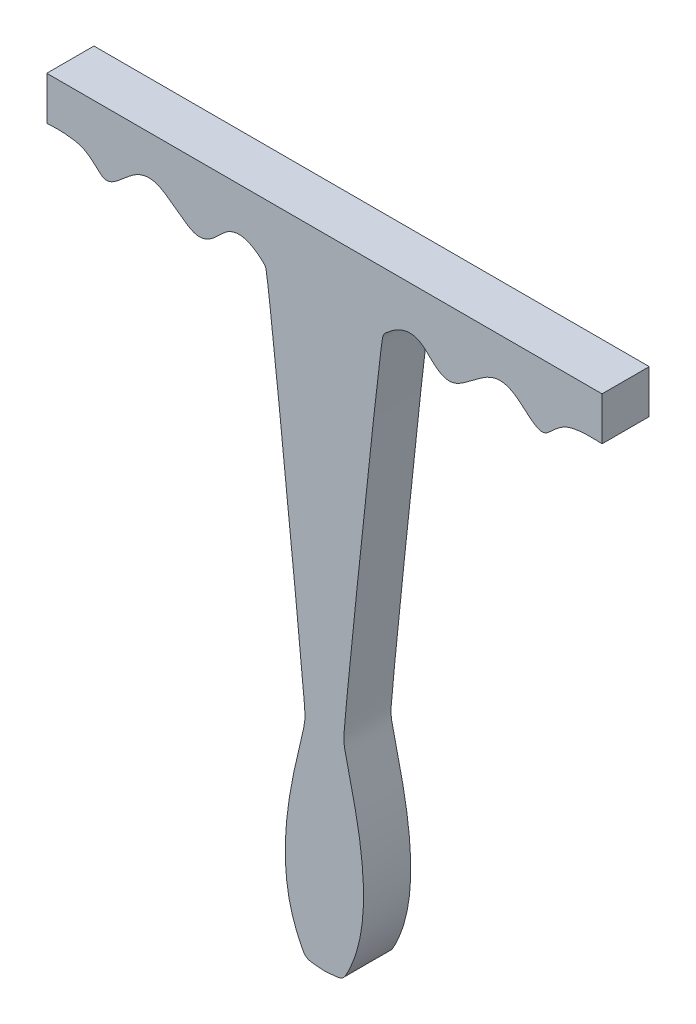
SolidWorks part; units mm, degrees
ref_plane "Plan de face" through (0, 0, 0) normal (0, 0, 1) x (1, 0, 0)
ref_plane "Plan de dessus" through (0, 0, 0) normal (0, 1, 0) x (1, 0, 0)
ref_plane "Plan de droite" through (0, 0, 0) normal (1, 0, 0) x (0, 0, -1)
sketch "Esquisse1" plane through (0, 0, 0) normal (0, 0, 1) x (1, 0, 0)
  line L0 (0, 0) -> (0, 1.7852) construction
  line L1 (0, 0) -> (0, 29.7342) construction
  line L2 (50, 24.2025) -> (-50, 24.2025)
  line L3 (-50, 24.2025) -> (-50, 16.4025)
  line L4 (50, 24.2025) -> (50, 16.4025)
  spline S0 degree 3 poles (-50, 16.4025) (-49.8421, 16.3861) (-42.4038, 17.1358) (-39.6187, 10.7861) (-33.9349, 17.4991) (-30.5564, 17.2857) (-26.8963, 14.9522) (-21.7768, 10.2494) (-16.6861, 18.7924) (-10.7283, 14.0803) (-10.0954, 12.8318) (-3.567, -49.8091) (-3.3281, -55.5258) (-9.9956, -75.8742) (-3.4964, -90.6478) (-2.9323, -90.597) (0, -90.7975) knots 0 0 0 0 0.017427 0.034313 0.051765 0.072769 0.077743 0.1015 0.145977 0.215724 0.261466 0.565409 0.636791 0.903902 0.943562 1 1 1 1
  spline S1 degree 3 poles (50, 16.4025) (49.8421, 16.3861) (42.4038, 17.1358) (39.6187, 10.7861) (33.9349, 17.4991) (30.5564, 17.2857) (26.8963, 14.9522) (21.7768, 10.2494) (16.6861, 18.7924) (10.7283, 14.0803) (10.0954, 12.8318) (3.567, -49.8091) (3.3281, -55.5258) (9.9956, -75.8742) (3.4964, -90.6478) (2.9323, -90.597) (0, -90.7975) knots 0 0 0 0 0.017427 0.034313 0.051765 0.072769 0.077743 0.1015 0.145977 0.215724 0.261466 0.565409 0.636791 0.903902 0.943562 1 1 1 1
  point P17 (0, 24.2025)
  dimension "D1" = 50
  dimension "D2" = 7.8
  dimension "D3" = 4.25
  dimension "D4" = 3.5
  dimension "D5" = 2
  dimension "D6" = 115
extrude "Boss.-Extru.1" add sketch "Esquisse1" along normal blind 8.5
equation "\"8.5.00mm\"=10"
